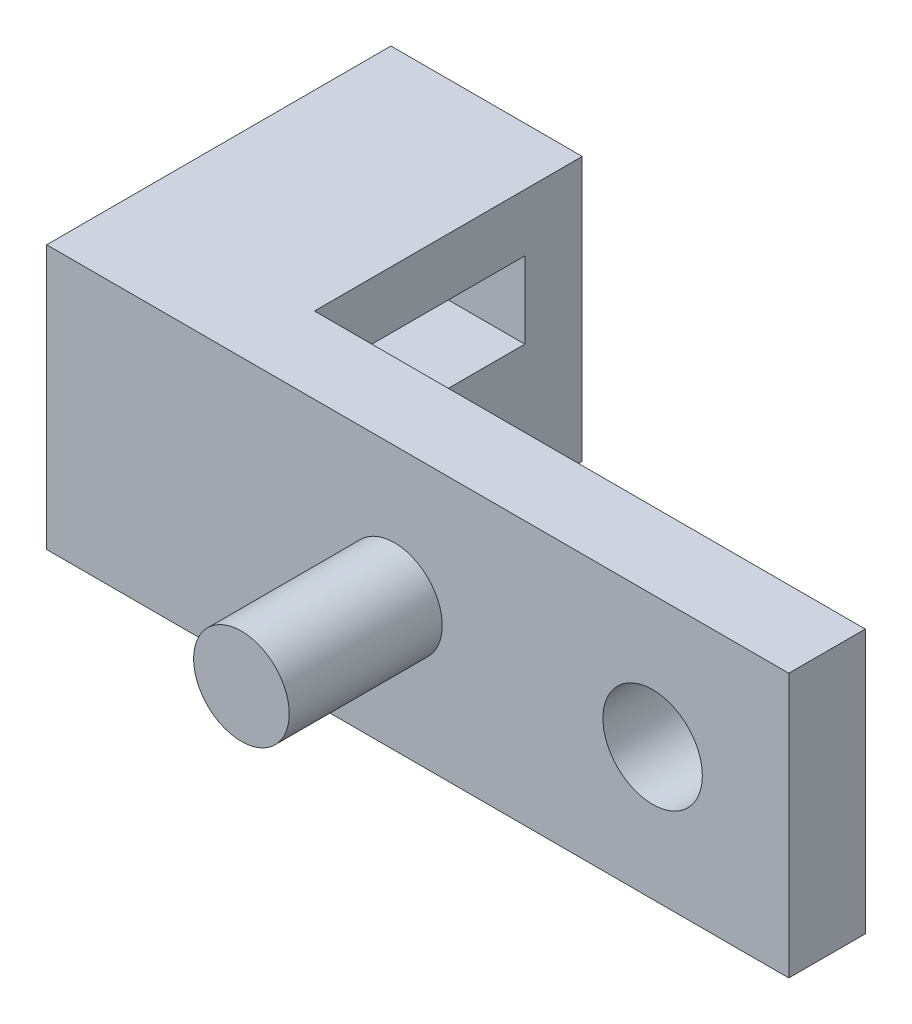
SolidWorks part; units mm, degrees
ref_plane "Front Plane" through (0, 0, 0) normal (0, 0, 1) x (1, 0, 0)
ref_plane "Top Plane" through (0, 0, 0) normal (0, 1, 0) x (1, 0, 0)
ref_plane "Right Plane" through (0, 0, 0) normal (1, 0, 0) x (0, 0, -1)
sketch "Sketch1" plane through (0, 0, 0) normal (0, 1, 0) x (1, 0, 0)
  line L0 (154.749, -21.0055) -> (135.349, -21.0055)
  line L1 (135.349, -21.0055) -> (135.349, -12.0055)
  line L2 (135.349, -12.0055) -> (140.349, -12.0055)
  line L3 (140.349, -12.0055) -> (140.349, -19.0055)
  line L4 (140.349, -19.0055) -> (154.749, -19.0055)
  line L5 (154.749, -19.0055) -> (154.749, -21.0055)
  dimension "D1" = 19.4
  dimension "D2" = 2
  dimension "D3" = 9
  dimension "D4" = 5
extrude "Boss-Extrude1" add sketch "Sketch1" along normal blind 6.9
sketch "Sketch2" plane through (0, 0, 21.0055) normal (0, 0, 1) x (1, 0, 0)
  line L0 (135.349, 6.9) -> (154.749, 6.9) construction
  line L1 (154.749, 6.9) -> (154.749, 0) construction
  circle A0 centre (151.189, 3.45) radius 1.3
  dimension "D1" = 3.45
  dimension "D2" = 2.6
  dimension "D3" = 3.56
extrude "Cut-Extrude1" cut sketch "Sketch2" against normal through all
sketch "Sketch3" plane through (0, 0, 21.0055) normal (0, 0, 1) x (1, 0, 0)
  circle A0 centre (144.439, 3.45) radius 1.25
  circle A1 centre (151.189, 3.45) radius 1.3 construction
  dimension "D1" = 2.5
  dimension "D2" = 6.75
extrude "Boss-Extrude2" add sketch "Sketch3" along normal blind 4
sketch "Sketch4" plane through (140.349, 0, 0) normal (1, 0, 0) x (0, 0, -1)
  line L1 (-17.5055, 3.4) -> (-13.5055, 3.4)
  line L2 (-17.5055, 3.4) -> (-17.5055, 5.4)
  line L3 (-17.5055, 5.4) -> (-13.5055, 5.4)
  line L4 (-13.5055, 3.4) -> (-13.5055, 5.4)
  line L5 (-12.0055, 6.9) -> (-12.0055, 0) construction
  line L6 (-19.0055, 6.9) -> (-12.0055, 6.9) construction
  dimension "D1" = 2
  dimension "D2" = 4
  dimension "D3" = 1.5
  dimension "D4" = 1.5
extrude "Cut-Extrude2" cut sketch "Sketch4" against normal through all
